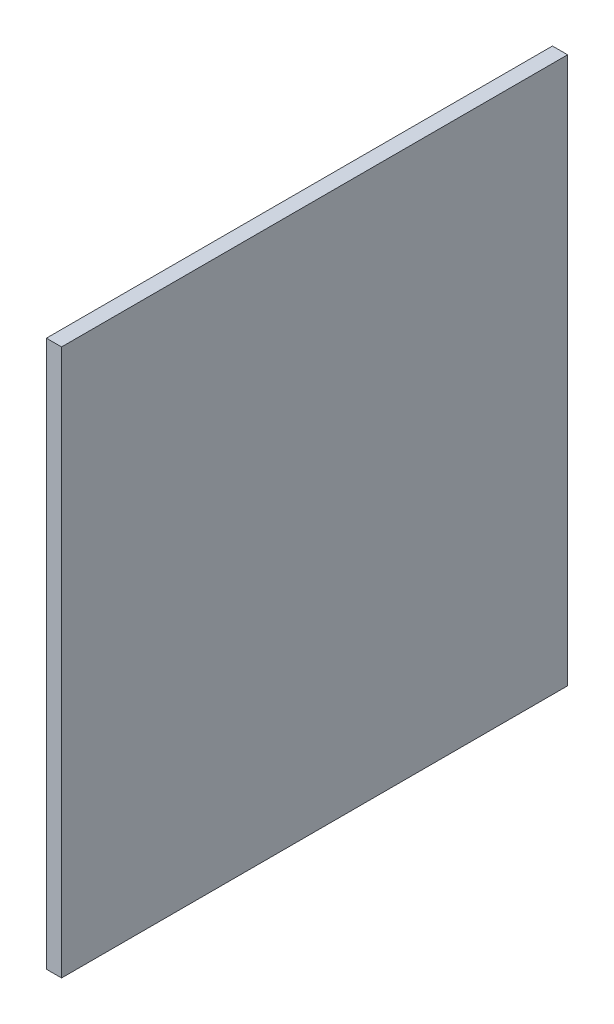
SolidWorks part; units mm, degrees
ref_plane "Front Plane" through (0, 0, 0) normal (0, 0, 1) x (1, 0, 0)
ref_plane "Top Plane" through (0, 0, 0) normal (0, 1, 0) x (1, 0, 0)
ref_plane "Right Plane" through (0, 0, 0) normal (1, 0, 0) x (0, 0, -1)
sketch "Sketch1" plane through (0, 0, 0) normal (0, 1, 0) x (1, 0, 0)
  line L1 (-0.75, 25) -> (0.75, 25)
  line L2 (-0.75, 25) -> (-0.75, -25)
  line L3 (-0.75, -25) -> (0.75, -25)
  line L4 (0.75, 25) -> (0.75, -25)
  line L5 (-0.75, 25) -> (0.75, -25) construction
  line L6 (-0.75, -25) -> (0.75, 25) construction
  point P0 (0, 0)
  dimension "D1" = 50
  dimension "D2" = 1.5
extrude "Boss-Extrude1" add sketch "Sketch1" along normal mid plane 54
